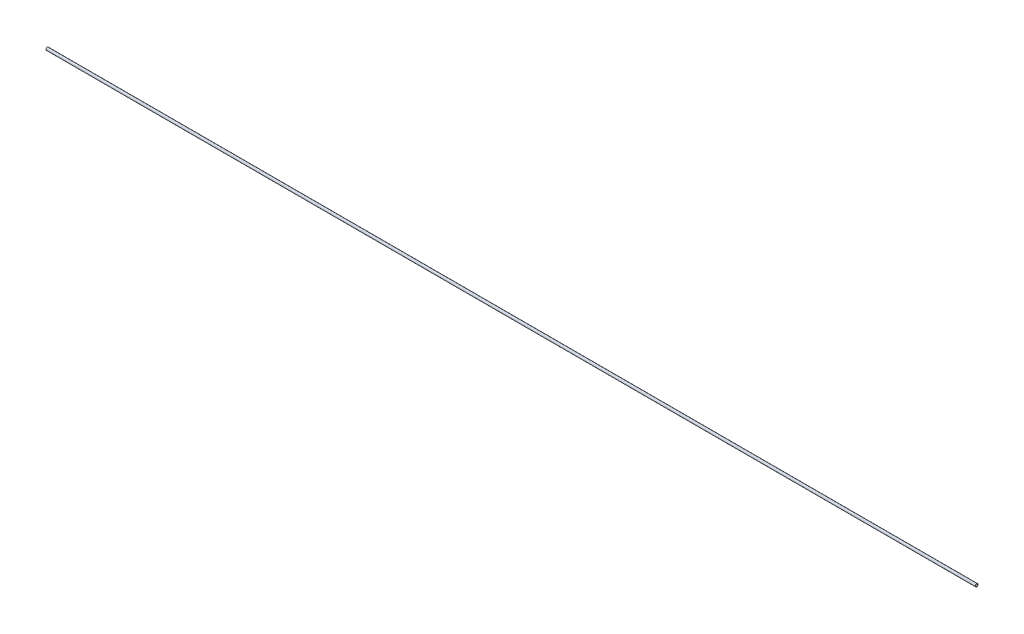
SolidWorks part; units mm, degrees
ref_plane "Front Plane" through (0, 0, 0) normal (0, 0, 1) x (1, 0, 0)
ref_plane "Top Plane" through (0, 0, 0) normal (0, 1, 0) x (1, 0, 0)
ref_plane "Right Plane" through (0, 0, 0) normal (1, 0, 0) x (0, 0, -1)
sketch "Sketch1" plane through (0, 0, 0) normal (1, 0, 0) x (0, 0, -1)
  circle A0 centre (0, 0) radius 2.3813
  circle A1 centre (0, 0) radius 1.8225
  dimension "D1" = 0.5588
  dimension "D2" = 4.7625
extrude "Boss-Extrude1" add sketch "Sketch1" along normal blind 1651
